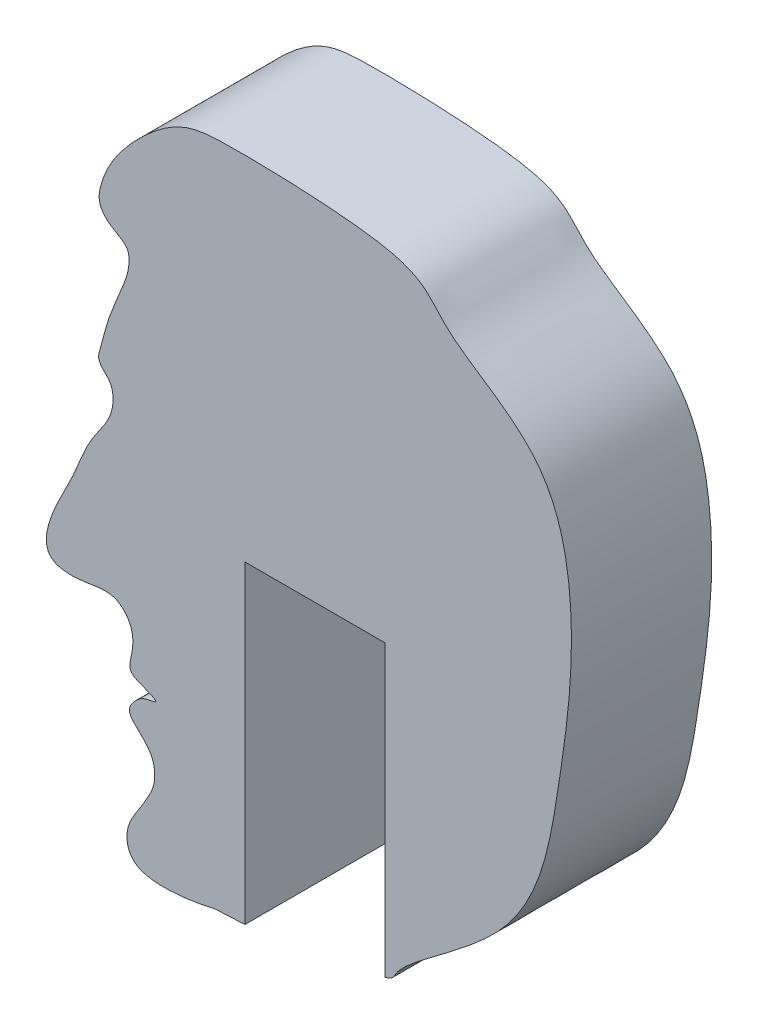
SolidWorks part; units mm, degrees
ref_plane "Front Plane" through (0, 0, 0) normal (0, 0, 1) x (1, 0, 0)
ref_plane "Top Plane" through (0, 0, 0) normal (0, 1, 0) x (1, 0, 0)
ref_plane "Right Plane" through (0, 0, 0) normal (1, 0, 0) x (0, 0, -1)
sketch "Sketch3" plane through (0, 0, 0) normal (0, 0, 1) x (1, 0, 0)
  line L0 (-7.0283, 0) -> (6.8711, 0) construction
  line L1 (0, 8.3019) -> (0, -11.3836) construction
  line L2 (1.8, -8.5505) -> (1.8, -2.3505)
  line L3 (-5.5, 5.5) -> (5.5, 5.5)
  line L4 (-5.5, 5.5) -> (-5.5, -9.5)
  line L5 (-5.5, -9.5) -> (5.5, -9.5)
  line L6 (1.8, -2.3505) -> (-1.2, -2.3505)
  line L7 (-1.2, -2.3505) -> (-1.2, -9.0709)
  spline S0 degree 3 poles (1.8, -8.5505) (1.9834, -8.4945) (2.0564, -8.0792) (4.9641, -6.4445) (5.5374, -3.1013) (5.9857, 0.112) (5.2974, 2.8321) (2.7132, 4.2057) (2.7901, 5.0737) (-1.2284, 5.2237) (-2.5924, 5.1425) (-3.621, 4.2871) (-4.2176, 3.4628) (-4.3556, 2.7486) (-4.0909, 2.4005) (-3.7102, 2.289) (-3.6524, 1.8421) (-3.8635, 1.3201) (-4.1492, 0.6671) (-4.2572, 0.1621) (-4.3465, -0.1219) (-4.2621, -0.3041) (-4.0766, -0.4241) (-3.9969, -0.7343) (-4.0746, -1.1932) (-4.5672, -1.7492) (-4.8228, -2.536) (-5.2477, -3.2856) (-5.6896, -4.4096) (-4.6431, -4.4956) (-4.0527, -4.2777) (-3.6032, -4.7126) (-3.5655, -5.13) (-3.7321, -5.6493) (-3.3871, -5.7299) (-3.0032, -5.9097) (-3.3773, -5.9391) (-3.5337, -6.0764) (-3.7617, -6.357) (-3.4207, -6.6584) (-3.134, -6.9606) (-3.1047, -7.4276) (-3.2818, -7.7666) (-3.4902, -8.1147) (-3.7827, -8.5224) (-3.6569, -9.4612) (-2.0645, -9.1591) (-1.8148, -9.0891) (-1.2904, -9.0787) (-1.2, -9.0709) knots 0.035721 0.035721 0.035721 0.035721 0.048111 0.116218 0.196216 0.287146 0.339828 0.38571 0.445307 0.49657 0.517294 0.547662 0.578023 0.585347 0.59344 0.605041 0.607153 0.622516 0.641305 0.65477 0.657234 0.660589 0.66715 0.67124 0.681073 0.696862 0.719663 0.733854 0.759567 0.772794 0.791588 0.797896 0.811274 0.818617 0.828456 0.832672 0.837705 0.843454 0.849076 0.857766 0.867553 0.877943 0.885823 0.89285 0.905031 0.918979 0.943845 0.947371 0.954241 0.954241 0.954241 0.954241
  dimension "D1" = 15
  dimension "D2" = 11
  dimension "D3" = 5.5
  dimension "D4" = 5.5
  dimension "D5" = 3
  dimension "D6" = 1.2
  dimension "D7" = 6.2
extrude "Boss-Extrude5" add sketch "Sketch3" along normal blind 3 contours L2 S0 L7 L6
